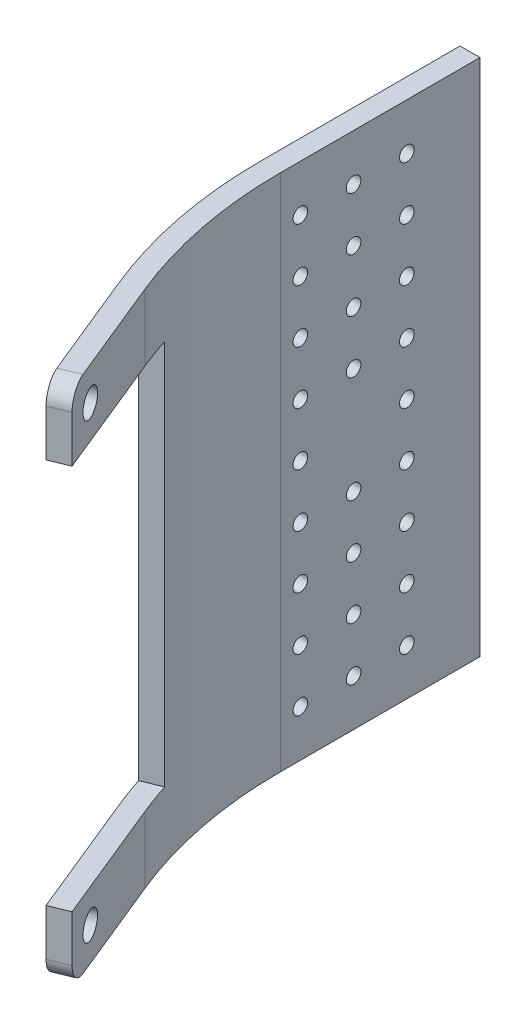
SolidWorks part; units mm, degrees
ref_plane "Face" through (0, 0, 0) normal (0, 0, 1) x (1, 0, 0)
ref_plane "Dessus" through (0, 0, 0) normal (0, 1, 0) x (1, 0, 0)
ref_plane "Droite" through (0, 0, 0) normal (1, 0, 0) x (0, 0, -1)
sketch "Esquisse1" plane through (0, 0, 0) normal (0, 1, 0) x (1, 0, 0)
  line L0 (0, 0) -> (0, 30)
  line L1 (0, 30) -> (3, 30)
  line L2 (3, 30) -> (3, 0)
  line L3 (5.2047, -26.487) -> (7.9816, -25.3519) construction
  line L4 (12.7724, -45) -> (15.5493, -43.8648)
  line L5 (5.2047, -26.487) -> (12.7724, -45)
  line L6 (7.9816, -25.3519) -> (15.5493, -43.8648)
  arc A0 (0, 0) -> (5.2047, -26.487) centre (70, 0) ccw
  arc A1 (3, 0) -> (7.9816, -25.3519) centre (70, 0) ccw
  dimension "D2" = 70
  dimension "D1" = 30
  dimension "D3" = 20
  dimension "D4" = 3
  dimension "D5" = 3
  dimension "D6" = 75
extrude "Extrusion1" add sketch "Esquisse1" along normal blind 78
sketch "Esquisse2" plane through (-4.8177, 0, 1.9694) normal (-0.9256, 0, 0.3784) x (0.3784, 0, 0.9256)
  line L0 (46.487, 39) -> (26.487, 39) construction
  line L1 (46.487, 78) -> (46.487, 0) construction
  line L2 (26.487, 78) -> (26.487, 0) construction
  line L3 (46.487, 68) -> (46.487, 10)
  line L4 (46.487, 10) -> (21.487, 10)
  line L5 (21.487, 10) -> (21.487, 68)
  line L6 (46.487, 68) -> (21.487, 68)
  line L7 (26.487, 0) -> (46.487, 0) construction
  line L8 (46.487, 39) -> (26.487, 39) construction
  line L9 (46.487, 78) -> (46.487, 0) construction
  line L10 (26.487, 78) -> (26.487, 0) construction
  circle A0 centre (41.487, 5) radius 2
  circle A1 centre (41.487, 73) radius 2
  point P10 (21.487, 39)
  dimension "D3" = 4
  dimension "D1" = 10
  dimension "D2" = 25
  dimension "D4" = 5
  dimension "D5" = 5
extrude "Extrusion3" cut sketch "Esquisse2" against normal up to next
fillet "Congé1" radius 3 2 edges at (14.1609, 0, 44.4324) (14.1609, 78, 44.4324)
sketch "Esquisse3" plane through (3, 0, 0) normal (1, 0, 0) x (0, 0, -1)
  line L0 (30, 39) -> (0, 39) construction
  line L1 (30, 78) -> (30, 0) construction
  line L2 (0, 78) -> (0, 0) construction
  line L3 (30, 31) -> (0, 31) construction
  line L4 (19, 39) -> (19, 0) construction
  line L5 (0, 0) -> (30, 0) construction
  line L6 (11, 39) -> (11, 0) construction
  line L7 (3, 39) -> (3, 0) construction
  line L8 (30, 23) -> (0, 23) construction
  line L9 (30, 15) -> (0, 15) construction
  line L10 (0, 7) -> (30, 7) construction
  circle A0 centre (3, 31) radius 1.1
  circle A1 centre (11, 31) radius 1.1
  circle A2 centre (19, 31) radius 1.1
  circle A3 centre (3, 39) radius 1.1
  circle A4 centre (19, 39) radius 1.1
  circle A5 centre (19, 47) radius 1.1
  circle A6 centre (11, 47) radius 1.1
  circle A7 centre (3, 47) radius 1.1
  circle A8 centre (3, 23) radius 1.1
  circle A9 centre (11, 23) radius 1.1
  circle A10 centre (19, 23) radius 1.1
  circle A11 centre (3, 15) radius 1.1
  circle A12 centre (11, 15) radius 1.1
  circle A13 centre (19, 15) radius 1.1
  circle A14 centre (3, 7) radius 1.1
  circle A15 centre (11, 7) radius 1.1
  circle A16 centre (19, 7) radius 1.1
  circle A17 centre (3, 71) radius 1.1
  circle A18 centre (3, 55) radius 1.1
  circle A19 centre (3, 63) radius 1.1
  circle A20 centre (11, 71) radius 1.1
  circle A21 centre (11, 63) radius 1.1
  circle A22 centre (11, 55) radius 1.1
  circle A23 centre (19, 55) radius 1.1
  circle A24 centre (19, 63) radius 1.1
  circle A25 centre (19, 71) radius 1.1
  dimension "D5" = 2.2
  dimension "D1" = 8
  dimension "D2" = 8
  dimension "D3" = 8
  dimension "D4" = 11
  dimension "D6" = 8
  dimension "D7" = 8
  dimension "D8" = 8
extrude "Extrusion4" cut sketch "Esquisse3" against normal up to next (3 mm away)
